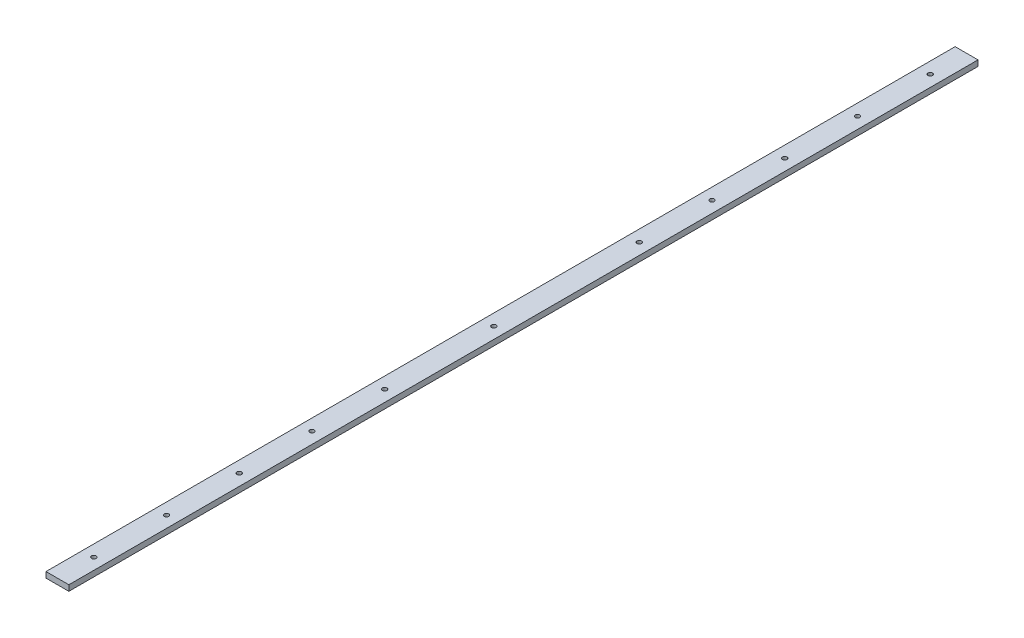
SolidWorks part; units mm, degrees
material "Copper"
ref_plane "Front Plane" through (0, 0, 0) normal (0, 0, 1) x (1, 0, 0)
ref_plane "Top Plane" through (0, 0, 0) normal (0, 1, 0) x (1, 0, 0)
ref_plane "Right Plane" through (0, 0, 0) normal (1, 0, 0) x (0, 0, -1)
sketch "Sketch1" plane through (0, 0, 0) normal (0, 1, 0) x (1, 0, 0)
  line L1 (0, 0) -> (12.7, 0)
  line L2 (0, 0) -> (0, 505)
  line L3 (0, 505) -> (12.7, 505)
  line L4 (12.7, 0) -> (12.7, 505)
  dimension "D1" = 12.7
  dimension "D2" = 505
extrude "Boss-Extrude1" add sketch "Sketch1" along normal blind 3.175
hole_wizard "Tap Drill for M3x0.5 Tap3" positions "Sketch7" profile "Sketch6" hole size "M3x0.5" standard "ANSI Metric"
sketch "Sketch7" plane through (0, 3.175, 0) normal (0, 1, 0) x (1, 0, 0)
  line L0 (6.35, 0) -> (6.35, 505) construction
  line L1 (0, 0) -> (12.7, 0) construction
  line L2 (12.7, 505) -> (0, 505) construction
  point P8 (6.35, 20.2)
  point P56 (6.35, 60.6)
  point P57 (6.35, 80.8) [skipped]
  point P58 (6.35, 101)
  point P60 (6.35, 141.4)
  point P61 (6.35, 161.6) [skipped]
  point P62 (6.35, 181.8)
  point P64 (6.35, 222.2) [skipped]
  point P65 (6.35, 242.4)
  point P66 (6.35, 262.6) [skipped]
  point P67 (6.35, 282.8) [skipped]
  point P69 (6.35, 323.2)
  point P70 (6.35, 343.4) [skipped]
  point P71 (6.35, 363.6)
  point P73 (6.35, 404)
  point P74 (6.35, 424.2) [skipped]
  point P75 (6.35, 444.4)
  point P77 (6.35, 484.8)
  point P100 (6.35, 40.4) [skipped]
  point P101 (6.35, 121.2) [skipped]
  point P102 (6.35, 202) [skipped]
  point P103 (6.35, 303) [skipped]
  point P104 (6.35, 383.8) [skipped]
  point P105 (6.35, 464.6) [skipped]
  dimension "D1" = 20.2
  dimension "D2" = 24
sketch "Sketch6" plane through (6.35, 3.175, -20.2) normal (1, 0, 0) x (0, 0, 1)
  line L0 (0, 0) -> (0, 12.4311)
  line L1 (0, 12.4311) -> (1.25, 11.68)
  line L2 (1.25, 11.68) -> (1.25, 0)
  line L5 (1.25, 0) -> (0, 0)
  line L10 (0, 12.4311) -> (-1.25, 11.68) construction
  line L11 (0, -6.35) -> (0, 107.95) construction
  dimension "Hole Dia." = 2.5
  dimension "Hole Depth" = 11.68
  dimension "Drill Angle" = 118
equation "\"ABS_thickness\" = 1.59\t"
equation "\"Bus_bar_thickness\" = 3.175"
equation "\"Connector_width\" = 20.2"
equation "\"Number_of_cells_long\" = 25"
equation "\"Number_of_cells_wide\" = 2"
equation "\"Cell_height\" = 65.0"
equation "\"Cell_diam\" = 18.0"
equation "\"D2@Sketch1\"=\"Number_of_cells_long\"*\"Connector_width\""
equation "\"D1@Boss-Extrude1\"=\"Bus_bar_thickness\""
equation "\"D1@Sketch7\" = \"Connector_width\""
